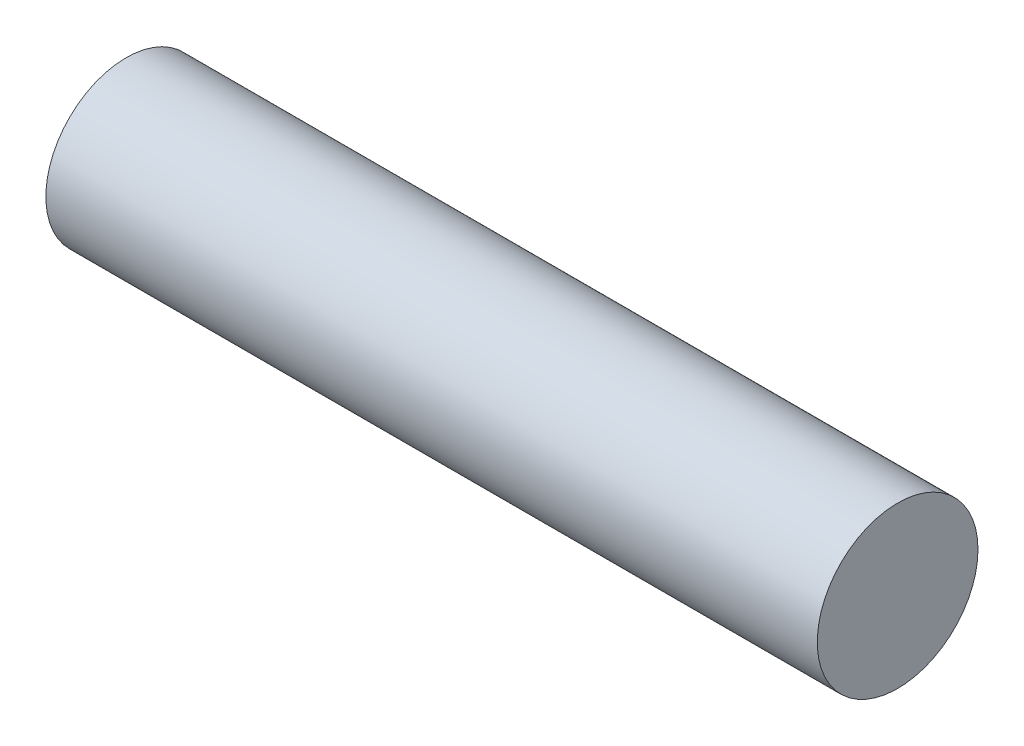
SolidWorks part; units mm, degrees
ref_plane "Front Plane" through (0, 0, 0) normal (0, 0, 1) x (1, 0, 0)
ref_plane "Top Plane" through (0, 0, 0) normal (0, 1, 0) x (1, 0, 0)
ref_plane "Right Plane" through (0, 0, 0) normal (1, 0, 0) x (0, 0, -1)
sketch "Sketch1" plane through (0, 0, 0) normal (0, 0, 1) x (1, 0, 0)
  line L0 (-19.05, 0) -> (19.05, 0) construction
  line L1 (-19.05, 3.9688) -> (-19.05, -3.9688) construction
  line L2 (19.05, 3.9688) -> (19.05, -3.9688) construction
  dimension "Diameter" = 7.9375
  dimension "Length" = 38.1
sketch "Sketch2" plane through (0, 0, 0) normal (1, 0, 0) x (0, 0, -1)
  circle A0 centre (0, 0) radius 3.9688
extrude "Extrude1" add sketch "Sketch2" against normal up to vertex (19.05 mm away) and the other way up to vertex (19.05 mm away) up to point (-19.05, 0, 0) other way up to point (19.05, 0, 0)
